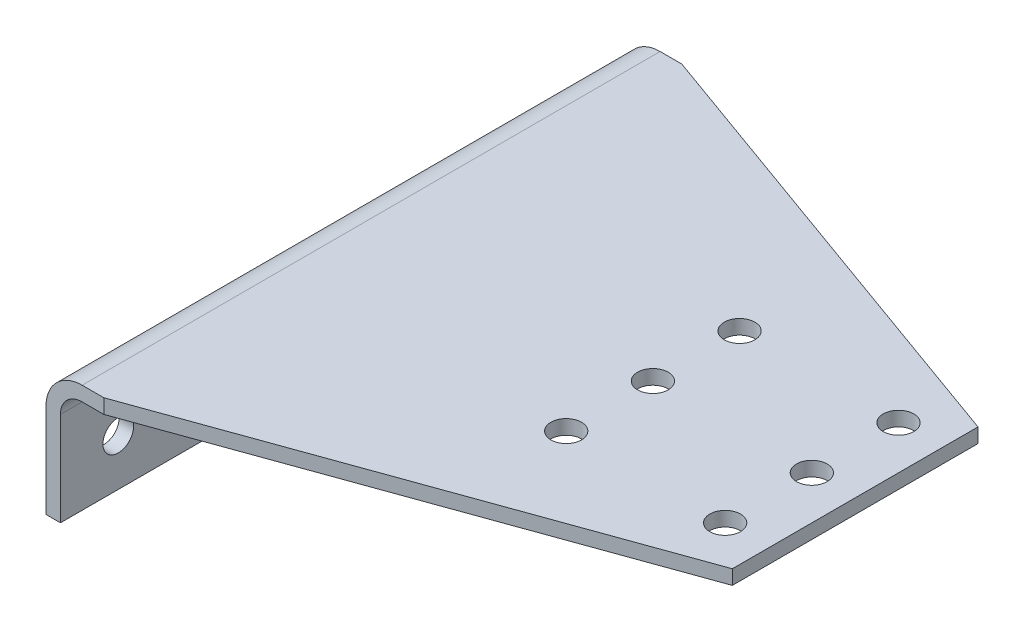
SolidWorks part; units mm, degrees
material "ASTM A36"
ref_plane "Front" through (0, 0, 0) normal (0, 0, 1) x (1, 0, 0)
ref_plane "Top" through (0, 0, 0) normal (0, 1, 0) x (1, 0, 0)
ref_plane "Side" through (0, 0, 0) normal (1, 0, 0) x (0, 0, -1)
sketch "Sketch1" plane through (0, 0, 0) normal (0, 0, 1) x (1, 0, 0)
  line L0 (228.6, 0) -> (15.875, 0)
  line L1 (0, -15.875) -> (0, -57.15)
  line L2 (0, -57.15) -> (6.35, -57.15)
  line L3 (6.35, -57.15) -> (6.35, -15.875)
  line L4 (15.875, -6.35) -> (228.6, -6.35)
  line L5 (228.6, -6.35) -> (228.6, 0)
  line L6 (50, 0) -> (-50, 0) construction
  arc A0 (15.875, 0) -> (0, -15.875) centre (15.875, -15.875) ccw
  arc A1 (6.35, -15.875) -> (15.875, -6.35) centre (15.875, -15.875) cw
  dimension "D3" = 9.525
  dimension "D1" = 228.6
  dimension "D2" = 57.15
  dimension "D4" = 6.35
extrude "Extrude1" add sketch "Sketch1" against normal mid plane 254
sketch "Sketch2" plane through (0, 0, 0) normal (0, 1, 0) x (1, 0, 0)
  line L0 (25.4, 127) -> (228.6, 53.975)
  line L1 (228.6, 127) -> (15.875, 127) construction
  line L2 (228.6, 127) -> (228.6, -127) construction
  line L3 (0, -50) -> (0, 50) construction
  line L4 (-50, 0) -> (50, 0) construction
  line L5 (0, 0) -> (258.8616, 0) construction
  line L6 (228.6, 53.975) -> (228.6, 127)
  line L7 (228.6, 127) -> (25.4, 127)
  line L8 (228.6, -53.975) -> (228.6, -127)
  line L9 (228.6, -127) -> (25.4, -127)
  line L10 (25.4, -127) -> (228.6, -53.975)
  line L11 (0, 0) -> (139.7, 0) construction
  line L12 (139.7, 0) -> (209.55, 0) construction
  line L13 (209.55, 0) -> (209.55, 38.1) construction
  line L14 (209.55, 38.1) -> (139.7, 38.1) construction
  line L15 (139.7, 38.1) -> (139.7, 0) construction
  circle A0 centre (209.55, 38.1) radius 6.731
  circle A1 centre (139.7, 38.1) radius 6.731
  circle A2 centre (209.55, 0) radius 6.731
  circle A3 centre (139.7, 0) radius 6.731
  circle A4 centre (139.7, -38.1) radius 6.731
  circle A5 centre (209.55, -38.1) radius 6.731
  dimension "D5" = 76.2
  dimension "D6" = 13.462
  dimension "D4" = 69.85
  dimension "D1" = 25.4
  dimension "D2" = 53.975
  dimension "D3" = 139.7
extrude "Cut-Chamfer" cut sketch "Sketch2" along normal blind 508 and the other way through all
sketch "Sketch3" plane through (0, 0, 0) normal (1, 0, 0) x (0, 0, -1)
  line L0 (101.6, -36.5125) -> (0, -36.5125) construction
  line L2 (50, 0) -> (-50, 0) construction
  line L3 (-14.7043, -93.6625) -> (186.8542, -93.6625) construction
  line L4 (0, 50) -> (0, -50) construction
  line L5 (0, -36.5125) -> (-101.6, -36.5125) construction
  line L6 (-101.6, -36.5125) -> (-101.6, -150.8125) construction
  line L7 (-101.6, -150.8125) -> (0, -150.8125) construction
  circle A0 centre (0, -36.5125) radius 6.731
  circle A1 centre (101.6, -36.5125) radius 6.731
  circle A2 centre (0, -150.8125) radius 6.731
  circle A3 centre (101.6, -150.8125) radius 6.731
  circle A4 centre (-101.6, -36.5125) radius 6.731
  circle A5 centre (-101.6, -150.8125) radius 6.731
  circle A6 centre (-50.8, -36.5125) radius 6.731
  circle A7 centre (50.8, -36.5125) radius 6.731
  circle A8 centre (50.8, -150.8125) radius 6.731
  circle A9 centre (-50.8, -150.8125) radius 6.731
  dimension "D2" = 101.6
  dimension "D3" = 13.462
  dimension "D6" = 50.8
  dimension "D7" = 50.8
  dimension "D8" = 50.8
  dimension "D9" = 50.8
  dimension "D1" = 101.6
  dimension "D4" = 36.5125
  dimension "D5" = 93.6625
extrude "Cut-Holes" cut sketch "Sketch3" along normal through all
